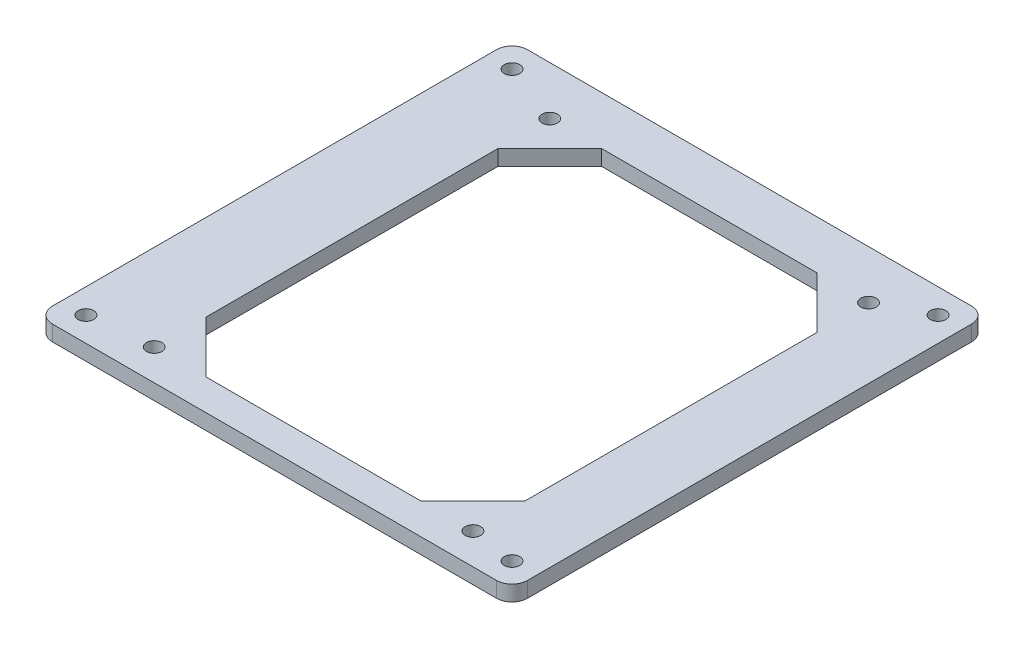
SolidWorks part; units mm, degrees
ref_plane "前基準面" through (0, 0, 0) normal (0, 0, 1) x (1, 0, 0)
ref_plane "上基準面" through (0, 0, 0) normal (0, 1, 0) x (1, 0, 0)
ref_plane "右基準面" through (0, 0, 0) normal (1, 0, 0) x (0, 0, -1)
ref_plane "平面1" through (0, 3, 0) normal (0, 1, 0) x (1, 0, 0)
sketch "草圖1" plane through (0, 3, 0) normal (0, 1, 0) x (1, 0, 0)
  line L0 (-46, 43) -> (-46, -43)
  line L1 (-43, -46) -> (43, -46)
  line L2 (46, -43) -> (46, 43)
  line L3 (43, 46) -> (-43, 46)
  line L4 (-19.285, 36.6) -> (22.435, 36.6)
  line L5 (22.435, 36.6) -> (32.435, 26.6)
  line L6 (32.435, 26.6) -> (32.435, -30)
  line L7 (32.435, -30) -> (22.435, -40)
  line L8 (22.435, -40) -> (-19.285, -40)
  line L9 (-19.285, -40) -> (-29.285, -30)
  line L10 (-29.285, -30) -> (-29.285, 26.6)
  line L11 (-29.285, 26.6) -> (-19.285, 36.6)
  arc A0 (-46, -43) -> (-43, -46) centre (-43, -43) ccw
  arc A1 (43, -46) -> (46, -43) centre (43, -43) ccw
  arc A2 (46, 43) -> (43, 46) centre (43, 43) ccw
  arc A3 (-43, 46) -> (-46, 43) centre (-43, 43) ccw
  circle A4 centre (-29.285, 36.6) radius 1.5
  circle A5 centre (32.435, 36.6) radius 1.5
  circle A6 centre (32.435, -40) radius 1.5
  circle A7 centre (-29.285, -40) radius 1.5
  circle A8 centre (41.25, -41.25) radius 1.5
  circle A9 centre (-41.25, 41.25) radius 1.5
  circle A10 centre (41.25, 41.25) radius 1.5
  circle A11 centre (-41.25, -41.25) radius 1.5
extrude "填料-伸長1" add sketch "草圖1" against normal blind 3
